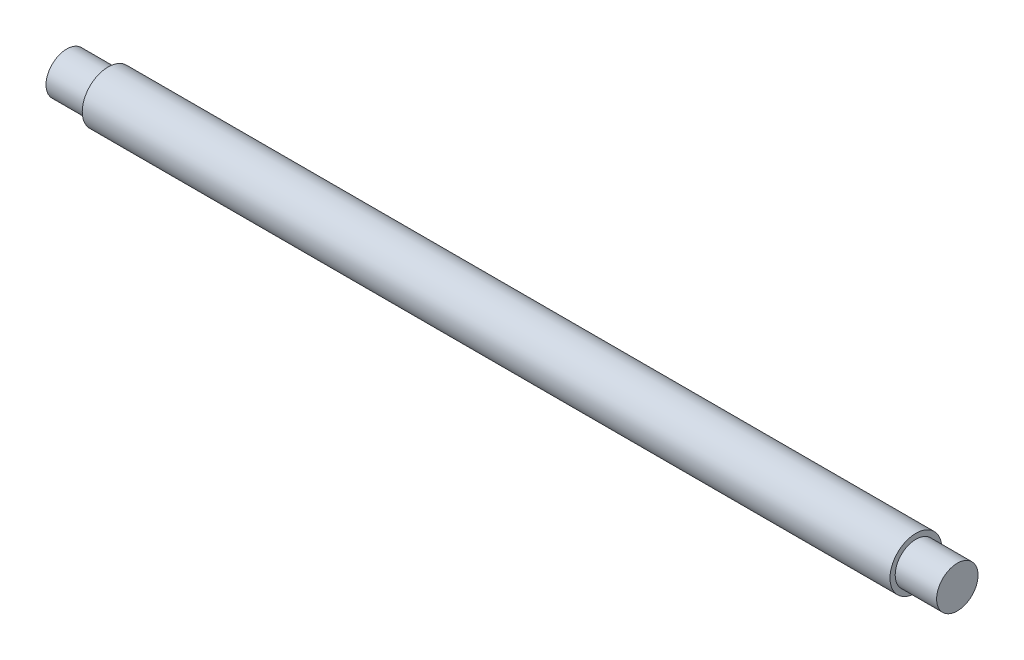
SolidWorks part; units mm, degrees
material "PBT General Purpose"
ref_plane "Front Plane" through (0, 0, 0) normal (0, 0, 1) x (1, 0, 0)
ref_plane "Top Plane" through (0, 0, 0) normal (0, 1, 0) x (1, 0, 0)
ref_plane "Right Plane" through (0, 0, 0) normal (1, 0, 0) x (0, 0, -1)
sketch "Sketch1" plane through (0, 0, 0) normal (0, 0, 1) x (1, 0, 0)
  line L0 (0, 0) -> (52.3219, 0) construction
  line L1 (0, 0) -> (0, 4)
  line L2 (0, 4) -> (8, 4)
  line L3 (8, 4) -> (8, 5)
  line L4 (8, 5) -> (164, 5)
  line L5 (164, 5) -> (164, 4)
  line L6 (164, 4) -> (172, 4)
  line L7 (172, 4) -> (172, 0)
  line L8 (0, 0) -> (172, 0)
  dimension "D1" = 8
  dimension "D2" = 4
  dimension "D3" = 5
  dimension "D4" = 4
  dimension "D5" = 8
  dimension "D6" = 172
revolve "Revolve1" add sketch "Sketch1" angle 360 about L0
